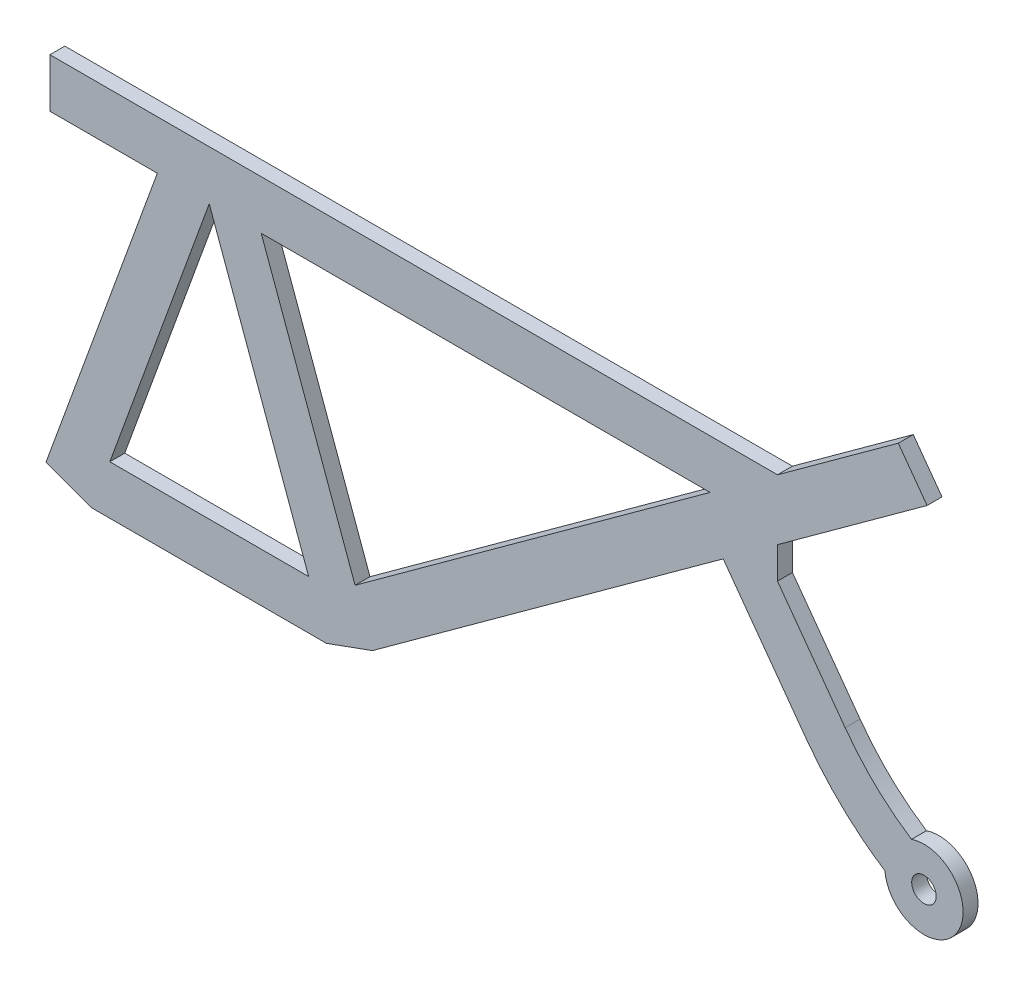
SolidWorks part; units mm, degrees
ref_plane "정면" through (0, 0, 0) normal (0, 0, 1) x (1, 0, 0)
ref_plane "윗면" through (0, 0, 0) normal (0, 1, 0) x (1, 0, 0)
ref_plane "우측면" through (0, 0, 0) normal (1, 0, 0) x (0, 0, -1)
sketch "Sketch1" plane through (0, 0, 0) normal (0, 0, 1) x (1, 0, 0)
  line L0 (0, 0) -> (71.6228, 52.037)
  line L1 (82.7118, 60.0937) -> (82.7118, 53.6447)
  line L2 (113.2624, 82.2899) -> (107.3845, 90.3801)
  line L3 (-3.558, 9.7756) -> (68.948, 62.4544)
  line L4 (82.7118, 72.4544) -> (107.3845, 90.3801)
  line L5 (-3.558, 9.7756) -> (-22.7315, 62.4544)
  line L6 (0, 0) -> (-9.3969, -3.4202)
  line L8 (104.704, 13.3419) -> (104.6585, 13.2714)
  line L12 (-66.6767, 0) -> (-57.2797, -3.4202)
  line L13 (-66.6767, 0) -> (-43.9451, 62.4544)
  line L14 (-13.0366, 6.5798) -> (-33.3383, 62.3583)
  line L16 (-9.3969, -3.4202) -> (-57.2797, -3.4202)
  line L18 (-13.0366, 6.5798) -> (-53.64, 6.5798)
  line L21 (-5.8779, 62.4544) -> (-22.7315, 62.4544)
  line L23 (-5.8779, 72.4544) -> (-65.8779, 72.4544)
  line L24 (-65.8779, 62.4544) -> (-65.8779, 72.4544)
  line L25 (-5.8779, 62.4544) -> (68.948, 62.4544)
  line L27 (-5.8779, 72.4544) -> (82.7118, 72.4544)
  line L34 (82.7118, 60.0937) -> (113.2624, 82.2899)
  line L35 (88.5017, 28.8053) -> (71.6228, 52.037)
  line L36 (96.524, 34.6338) -> (82.7118, 53.6447)
  line L37 (-43.9451, 62.4544) -> (-65.8779, 62.4544)
  line L39 (-53.64, 6.5798) -> (-33.3383, 62.3583)
  circle A0 centre (112.6176, 14.0798) radius 2.5
  arc A1 (104.6585, 13.2714) -> (110.0877, 21.6693) centre (112.6176, 14.0798) ccw
  spline S0 degree 3 poles (88.5017, 28.8053) (92.967, 22.6593) (98.4106, 17.4106) (104.704, 13.3419) knots 0.5 0.5 0.5 0.5 0.915854 0.915854 0.915854 0.915854
  spline S1 degree 1 poles (96.524, 34.6338) (110.0877, 21.6693) knots 0 0 1 1 construction
  spline S2 degree 3 poles (96.524, 34.6338) (97.4637, 33.3405) (99.4673, 30.8207) (103.8154, 26.2627) (107.4763, 23.3576) (110.0877, 21.6693) knots 0.5 0.5 0.5 0.5 0.603963 0.707927 0.915854 0.915854 0.915854 0.915854
extrude "Boss-Extrude1" add sketch "Sketch1" along normal blind 3.048
